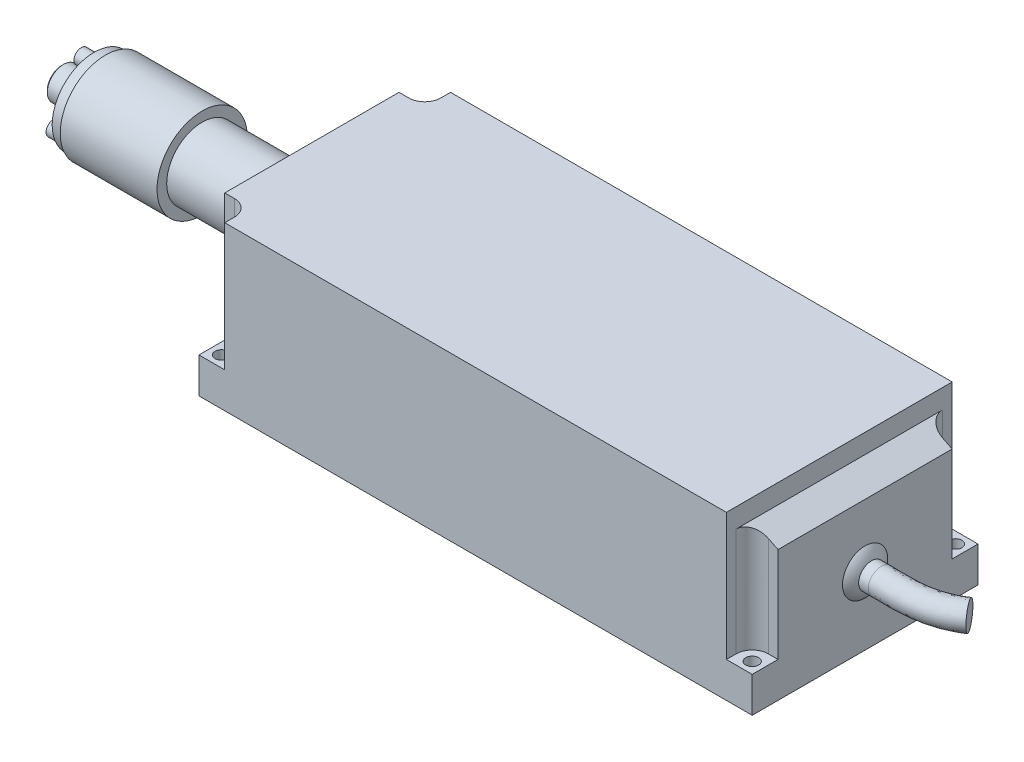
SolidWorks part; units mm, degrees
ref_plane "Front Plane" through (0, 0, 0) normal (0, 0, 1) x (1, 0, 0)
ref_plane "Top Plane" through (0, 0, 0) normal (0, 1, 0) x (1, 0, 0)
ref_plane "Right Plane" through (0, 0, 0) normal (1, 0, 0) x (0, 0, -1)
sketch "Sketch1" plane through (0, 0, 0) normal (0, 1, 0) x (1, 0, 0)
  line L1 (0, -35) -> (171.5, -35)
  line L2 (0, -35) -> (0, 35)
  line L3 (0, 35) -> (171.5, 35)
  line L4 (171.5, -35) -> (171.5, 35)
  dimension "D1" = 70
  dimension "D2" = 171.5
extrude "Boss-Extrude1" add sketch "Sketch1" along normal blind 11
sketch "Sketch2" plane through (0, 11, 0) normal (0, 1, 0) x (1, 0, 0)
  line L0 (0, 27) -> (0, -27)
  line L1 (0, 35) -> (0, -35) construction
  line L2 (0, 27) -> (8, 27)
  line L3 (8, 27) -> (8, 35)
  line L4 (171.5, 35) -> (0, 35) construction
  line L5 (8, 35) -> (163.5, 35)
  line L6 (163.5, 35) -> (163.5, 27)
  line L7 (163.5, 27) -> (171.5, 27)
  line L8 (171.5, -35) -> (171.5, 35) construction
  line L9 (171.5, 27) -> (171.5, -27)
  line L10 (171.5, -27) -> (163.5, -27)
  line L11 (163.5, -27) -> (163.5, -35)
  line L12 (0, -35) -> (171.5, -35) construction
  line L13 (163.5, -35) -> (8, -35)
  line L14 (8, -35) -> (8, -27)
  line L15 (8, -27) -> (0, -27)
  dimension "D1" = 8
extrude "Boss-Extrude2" add sketch "Sketch2" along normal blind 39.5
fillet "Fillet1" radius 5 4 edges at (163.5, 30.75, -27) (163.5, 30.75, 27) (8, 30.75, 27) (8, 30.75, -27)
sketch "Sketch3" plane through (0, 50.5, 0) normal (0, 1, 0) x (1, 0, 0)
  line L10 (171.5, 35) -> (163.5, 35)
  line L11 (171.5, 35) -> (171.5, -35)
  line L12 (171.5, -35) -> (163.5, -35)
  line L13 (163.5, 35) -> (163.5, -35)
extrude "Cut-Extrude1" cut sketch "Sketch3" against normal blind 6
sketch "Sketch4" plane through (0, 0, 35) normal (0, 0, 1) x (1, 0, 0)
  line L0 (163.5, 44.5) -> (171.5, 40.5)
  line L1 (171.5, 44.5) -> (171.5, 11) construction
  line L2 (171.5, 40.5) -> (171.5, 44.5)
  line L3 (171.5, 44.5) -> (163.5, 44.5)
  dimension "D1" = 4
extrude "Cut-Extrude2" cut sketch "Sketch4" against normal up to next
sketch "Sketch5" plane through (0, 0, 0) normal (-1, 0, 0) x (0, 0, 1)
  line L0 (-12.9518, 40.5) -> (12.9518, 40.5)
  line L1 (-12.9518, 15.5) -> (12.9518, 15.5)
  line L2 (-27, 50.5) -> (27, 50.5) construction
  arc A0 (-12.9518, 40.5) -> (-12.9518, 15.5) centre (0, 28) ccw
  arc A1 (12.9518, 40.5) -> (12.9518, 15.5) centre (0, 28) cw
  point P4 (0, 15.5)
  point P5 (0, 40.5)
  dimension "D2" = 18
  dimension "D1" = 25
  dimension "D3" = 10
extrude "Boss-Extrude3" add sketch "Sketch5" along normal blind 3 separate body
sketch "Sketch6" plane through (-3, 0, 0) normal (-1, 0, 0) x (0, 0, 1)
  circle A0 centre (0, 28) radius 11
  arc A1 (-12.9518, 40.5) -> (-12.9518, 15.5) centre (0, 28) ccw construction
  dimension "D1" = 22
extrude "Boss-Extrude4" add sketch "Sketch6" along normal blind 31
sketch "Sketch7" plane through (-34, 0, 0) normal (-1, 0, 0) x (0, 0, 1)
  circle A0 centre (0, 28) radius 14
  circle A1 centre (0, 28) radius 11 construction
  dimension "D1" = 28
extrude "Boss-Extrude5" add sketch "Sketch7" along normal blind 30 separate body
sketch "Sketch8" plane through (-64, 0, 0) normal (-1, 0, 0) x (0, 0, 1)
  circle A0 centre (0, 28) radius 13
  circle A1 centre (0, 28) radius 14 construction
  dimension "D1" = 26
extrude "Boss-Extrude6" add sketch "Sketch8" along normal blind 3.5 separate body
sketch "Sketch9" plane through (-67.5, 0, 0) normal (-1, 0, 0) x (0, 0, 1)
  circle A0 centre (0, 38) radius 2.25
  circle A1 centre (8.6603, 23) radius 2.25
  circle A2 centre (-8.6603, 23) radius 2.25
  point P2 (0, 28)
  point P10 (0, 28)
  dimension "D1" = 4.5
  dimension "D2" = 10
  dimension "D3" = 3
extrude "Boss-Extrude7" add sketch "Sketch9" along normal blind 4
sketch "Sketch10" plane through (-71.5, 0, 0) normal (-1, 0, 0) x (0, 0, 1)
  line L1 (1.5, 37.134) -> (1.5, 38.866)
  line L2 (1.5, 38.866) -> (0, 39.7321)
  line L3 (0, 39.7321) -> (-1.5, 38.866)
  line L4 (-1.5, 38.866) -> (-1.5, 37.134)
  line L5 (-1.5, 37.134) -> (0, 36.2679)
  line L6 (0, 36.2679) -> (1.5, 37.134)
  line L7 (10.1603, 23.866) -> (8.6603, 24.7321)
  line L8 (8.6603, 24.7321) -> (7.1603, 23.866)
  line L9 (7.1603, 23.866) -> (7.1603, 22.134)
  line L10 (7.1603, 22.134) -> (8.6603, 21.2679)
  line L11 (8.6603, 21.2679) -> (10.1603, 22.134)
  line L12 (10.1603, 22.134) -> (10.1603, 23.866)
  line L13 (-7.1603, 23.866) -> (-8.6603, 24.7321)
  line L14 (-8.6603, 24.7321) -> (-10.1603, 23.866)
  line L15 (-10.1603, 23.866) -> (-10.1603, 22.134)
  line L16 (-10.1603, 22.134) -> (-8.6603, 21.2679)
  line L17 (-8.6603, 21.2679) -> (-7.1603, 22.134)
  line L18 (-7.1603, 22.134) -> (-7.1603, 23.866)
  circle A0 centre (0, 38) radius 1.5 construction
  circle A1 centre (8.6603, 23) radius 1.5 construction
  circle A2 centre (-8.6603, 23) radius 1.5 construction
  dimension "D1" = 3
extrude "Cut-Extrude3" cut sketch "Sketch10" against normal blind 3
sketch "Sketch11" plane through (-67.5, 0, 0) normal (-1, 0, 0) x (0, 0, 1)
  circle A0 centre (0, 28) radius 4.5
  circle A1 centre (0, 28) radius 13 construction
  dimension "D1" = 9
extrude "Boss-Extrude8" add sketch "Sketch11" along normal blind 4 separate body
sketch "Sketch12" plane through (-71.5, 0, 0) normal (-1, 0, 0) x (0, 0, 1)
  circle A0 centre (0, 28) radius 5
  dimension "D1" = 10
extrude "Boss-Extrude9" add sketch "Sketch12" along normal blind 6
chamfer "Chamfer1" distance 0.5 angle 45 1 edges at (-77.5, 28, 5)
sketch "Sketch13" plane through (0, 11, 0) normal (0, 1, 0) x (1, 0, 0)
  line L0 (171.5, 35) -> (163.5, 35) construction
  line L1 (171.5, 27) -> (171.5, 35) construction
  line L2 (163.5, -35) -> (171.5, -35) construction
  line L3 (0, -27) -> (0, -35) construction
  circle A0 centre (3.5, 31.5) radius 2
  circle A1 centre (3.5, -31.5) radius 2
  circle A2 centre (168, -31.5) radius 2
  circle A3 centre (168, 31.5) radius 2
  dimension "D1" = 4
  dimension "D2" = 3.5
  dimension "D3" = 3.5
  dimension "D4" = 3.5
  dimension "D5" = 3.5
extrude "Cut-Extrude4" cut sketch "Sketch13" against normal up to next (11 mm away)
sketch "Sketch14" plane through (0, 50.5, 0) normal (0, 1, 0) x (1, 0, 0)
  line L0 (52.2179, -21.475) -> (52.2179, 29.8864) construction
sketch "Sketch15" plane through (171.5, 0, 0) normal (1, 0, 0) x (0, 0, -1)
  circle A0 centre (0, 21) radius 4
  dimension "D1" = 8
  dimension "D2" = 21
sketch3d "3DSketch1"
  line L0 (171.5, 21, 0) -> (176.5, 21, 0)
  spline S0 degree 3 poles (176.5, 21, 0) (179.3642, 21, 0) (187.3837, 21, 0.38) (195.2764, 21, -1.6984) (199.376, 21, -4.4604) knots 0 0 0 0 0.374776 1 1 1 1
  dimension "D1" = 5
sweep "Sweep1" add profiles "Sketch15" path "3DSketch1"
sketch "Sketch16" plane through (0, 0, 0) normal (0, 0, 1) x (1, 0, 0)
  line L0 (171.5, 25) -> (171.5, 28)
  line L1 (171.5, 40.5) -> (171.5, 11) construction
  line L2 (176.5, 25) -> (171.5, 25) construction
  line L3 (171.5, 25) -> (173.5, 25)
  arc A1 (171.5, 28) -> (173.5, 25) centre (166.4426, 22.4617) cw
  dimension "D3" = 7.5
  dimension "D1" = 2
  dimension "D2" = 3
revolve "Revolve1" add sketch "Sketch16" angle 360 about L0
